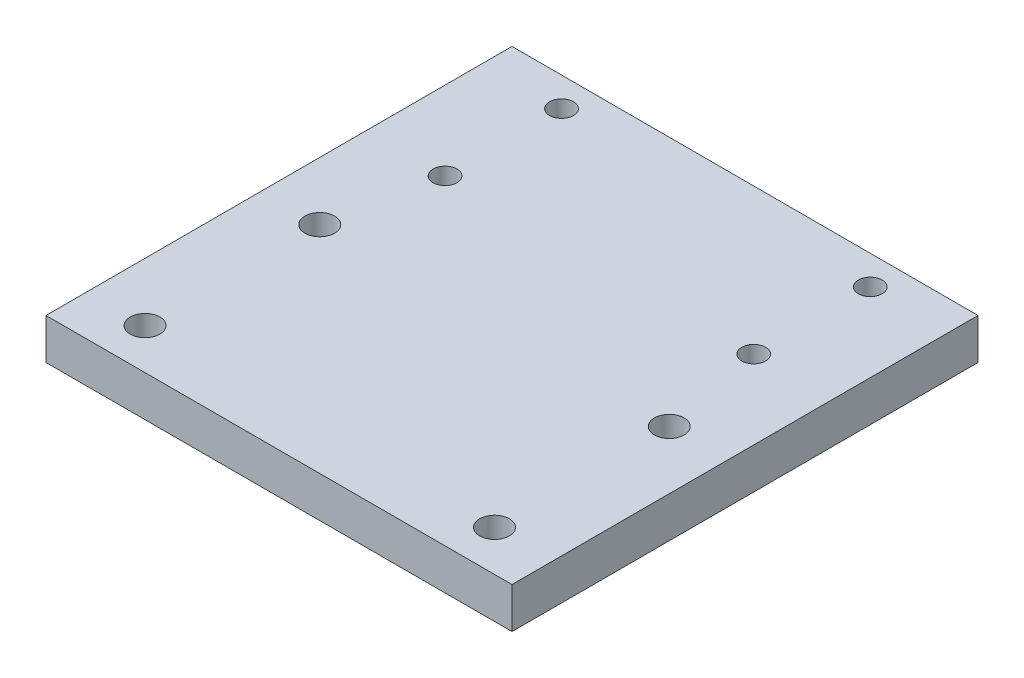
SolidWorks part; units mm, degrees
ref_plane "Front Plane" through (0, 0, 0) normal (0, 0, 1) x (1, 0, 0)
ref_plane "Top Plane" through (0, 0, 0) normal (0, 1, 0) x (1, 0, 0)
ref_plane "Right Plane" through (0, 0, 0) normal (1, 0, 0) x (0, 0, -1)
sketch "Sketch1" plane through (0, 0, 0) normal (0, 1, 0) x (1, 0, 0)
  line L0 (0, 58) -> (0, -22) construction
  line L1 (-40, 58) -> (40, 58)
  line L2 (-40, 58) -> (-40, -22)
  line L4 (40, 58) -> (40, -22)
  line L5 (-40, 58) -> (15.1724, -22) construction
  line L6 (-15.1724, -22) -> (40, 58) construction
  line L7 (-26.5, 33) -> (-26.5, 53) construction
  line L8 (-26.5, 53) -> (26.5, 53) construction
  line L9 (26.5, 53) -> (26.5, 33) construction
  line L10 (26.5, 33) -> (-26.5, 33) construction
  line L11 (-40, -22) -> (40, -22)
  circle A0 centre (-30, 15) radius 2.55
  circle A1 centre (30, 15) radius 2.55
  circle A2 centre (30, -15) radius 2.55
  circle A3 centre (-30, -15) radius 2.55
  circle A4 centre (-26.5, 53) radius 2.05
  circle A5 centre (26.5, 53) radius 2.05
  circle A6 centre (26.5, 33) radius 2.05
  circle A7 centre (-26.5, 33) radius 2.05
  point P0 (0, 0)
  dimension "D3" = 5.1
  dimension "D6" = 4.1
  dimension "D1" = 80
  dimension "D2" = 80
  dimension "D4" = 60
  dimension "D5" = 30
  dimension "D7" = 5
  dimension "D8" = 15
  dimension "D9" = 7
extrude "Boss-Extrude1" add sketch "Sketch1" along normal blind 7
hole_wizard "CBORE for 5/64 Ejector Pin1" positions "Sketch4" profile "Sketch5" counterbore size "5/64" standard "Superior" end condition through all
sketch "Sketch4" plane through (0, 0, 0) normal (0, -1, 0) x (-1, 0, 0)
  point P0 (26.5, 33)
  point P3 (-26.5, 33)
  point P6 (26.5, 53)
  point P9 (-26.5, 53)
sketch "Sketch5" plane through (-26.5, 0, -33) normal (1, 0, 0) x (0, 0, -1)
  line L0 (0, 0) -> (0, 7)
  line L1 (0, 7) -> (0.9922, 7)
  line L3 (0.9922, 7) -> (0.9922, 2.175)
  line L4 (0.9922, 2.175) -> (2.9766, 2.175)
  line L5 (2.9766, 2.175) -> (2.9766, 0)
  line L7 (2.9766, 0) -> (0, 0)
  line L11 (0, -6.35) -> (0, 107.95) construction
  dimension "Thru Hole Dia." = 1.9844
  dimension "Thru Hole Depth" = 7
  dimension "C'Bore Dia." = 5.9531
  dimension "C'Bore Depth" = 2.175
